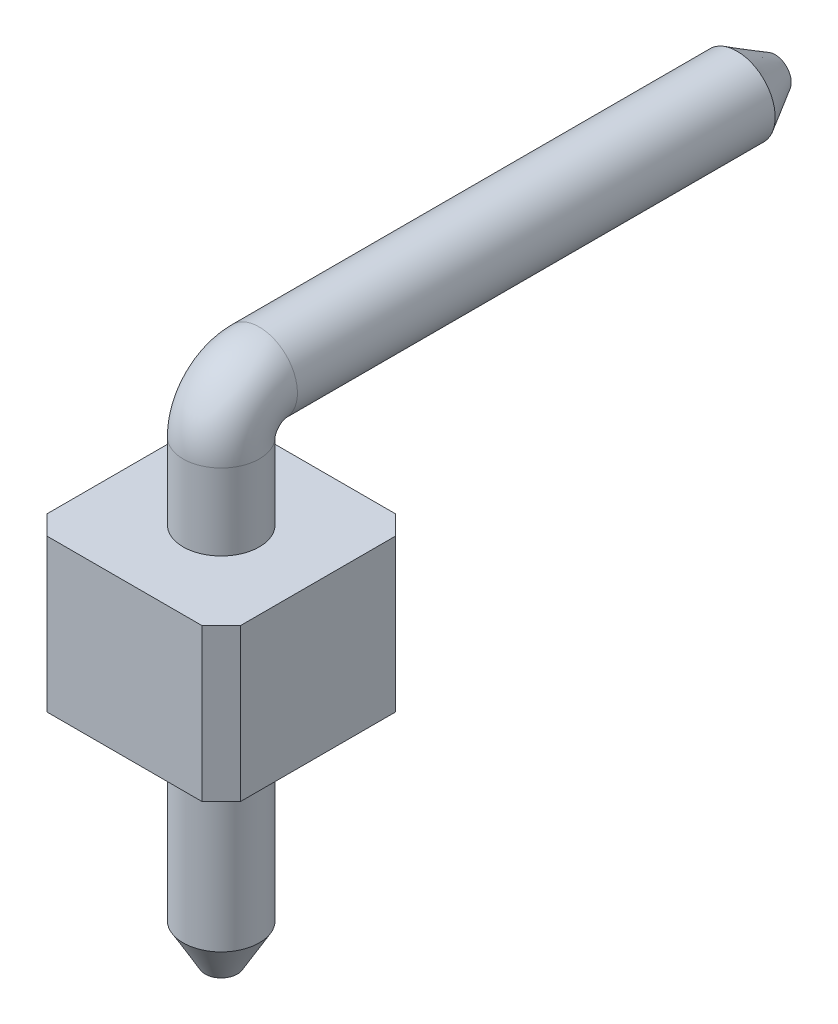
SolidWorks part; units mm, degrees
ref_plane "Front Plane" through (0, 0, 0) normal (0, 0, 1) x (1, 0, 0)
ref_plane "Top Plane" through (0, 0, 0) normal (0, 1, 0) x (1, 0, 0)
ref_plane "Right Plane" through (0, 0, 0) normal (1, 0, 0) x (0, 0, -1)
sketch "Sketch1" plane through (0, 0, 0) normal (0, 1, 0) x (1, 0, 0)
  line L1 (-1.27, 1.27) -> (1.27, 1.27)
  line L2 (-1.27, 1.27) -> (-1.27, -1.27)
  line L3 (-1.27, -1.27) -> (1.27, -1.27)
  line L4 (1.27, 1.27) -> (1.27, -1.27)
  line L5 (-1.27, 1.27) -> (1.27, -1.27) construction
  line L6 (-1.27, -1.27) -> (1.27, 1.27) construction
  point P0 (0, 0)
  dimension "D1" = 2.54
  dimension "D2" = 2.54
extrude "Boss-Extrude1" add sketch "Sketch1" along normal blind 2
chamfer "Chamfer1" distance 0.25 angle 45 4 edges at (-1.27, 1, -1.27) (-1.27, 1, 1.27) (1.27, 1, -1.27) (1.27, 1, 1.27)
sketch "Sketch2" plane through (0, 2, 0) normal (0, 1, 0) x (1, 0, 0)
  circle A0 centre (0, 0) radius 0.5
  dimension "D1" = 1
sketch "Sketch3" plane through (0, 0, 0) normal (0, -1, 0) x (1, 0, 0)
  circle A0 centre (0, 0) radius 0.5
  dimension "D1" = 1
extrude "Boss-Extrude3" add sketch "Sketch3" along normal blind 3
chamfer "Chamfer3" distance 0.5 angle 30 1 edges at (0, -3, -0.5)
sketch "Sketch4" plane through (0, 0, 0) normal (1, 0, 0) x (0, 0, -1)
  line L0 (0, 2.5096) -> (0, 6.8914) construction
  line L1 (0, 2) -> (0, 3)
  line L3 (-1.02, 2) -> (1.02, 2) construction
  line L4 (0.5, 3.5) -> (7.27, 3.5)
  arc A0 (0, 3) -> (0.5, 3.5) centre (0.5, 3) cw
  dimension "D3" = 6.77
  dimension "D1" = 1
  dimension "D2" = 0.5
sweep "Sweep1" add profiles "Sketch2" path "Sketch4"
chamfer "Chamfer4" distance 0.5 angle 30 1 edges at (0, 4, -7.27)
